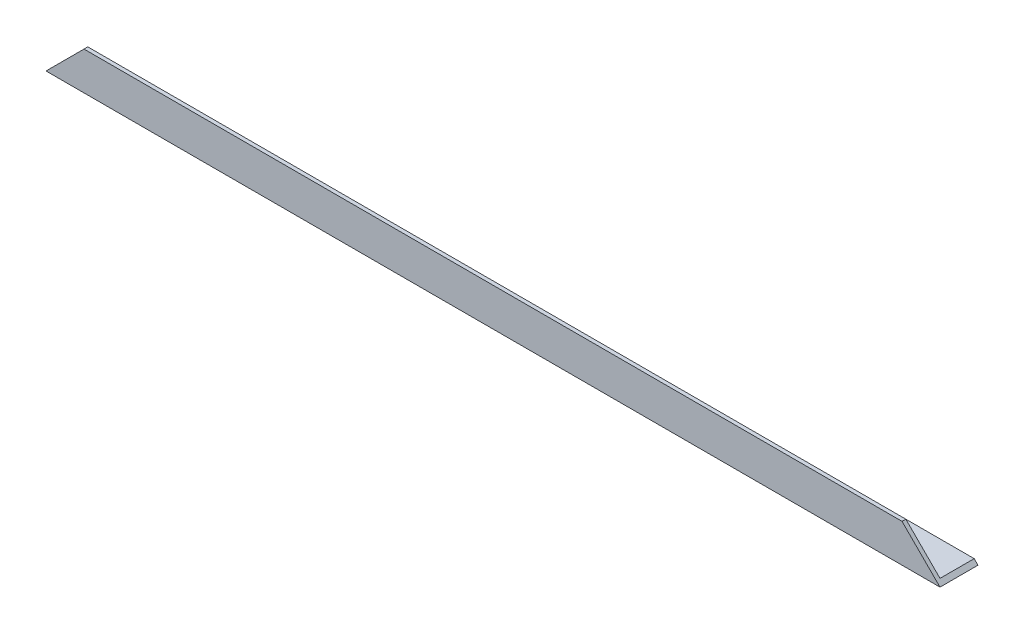
SolidWorks part; units mm, degrees
ref_plane "Спереди" through (0, 0, 0) normal (0, 0, 1) x (1, 0, 0)
ref_plane "Сверху" through (0, 0, 0) normal (0, 1, 0) x (1, 0, 0)
ref_plane "Справа" through (0, 0, 0) normal (1, 0, 0) x (0, 0, -1)
sketch "Эскиз1" plane through (0, 0, 0) normal (1, 0, 0) x (0, 0, -1)
  line L0 (0, 0) -> (0, 15)
  line L1 (0, 15) -> (1.5, 15)
  line L2 (1.5, 15) -> (1.5, 1.5)
  line L3 (1.5, 1.5) -> (15, 1.5)
  line L4 (15, 1.5) -> (15, 0)
  line L5 (15, 0) -> (0, 0)
  dimension "D1" = 15
  dimension "D2" = 15
  dimension "D3" = 1.5
  dimension "D4" = 1.5
extrude "Бобышка-Вытянуть1" add sketch "Эскиз1" along normal blind 353
ref_plane "Плоскость1" through (176.5, 0, 0) normal (-1, 0, 0) x (0, 0, 1)
sketch "Эскиз2" plane through (0, 0, 0) normal (0, 0, 1) x (1, 0, 0)
  line L0 (0, 0) -> (21.7299, 21.7299)
  line L1 (21.7299, 21.7299) -> (0, 21.7299)
  line L2 (0, 21.7299) -> (0, 0)
  dimension "D1" = 45
extrude "Вырез-Вытянуть1" cut sketch "Эскиз2" against normal through all
mirror "Зеркальное отражение1" about plane through (176.5, 0, 0) normal (-1, 0, 0) of "Вырез-Вытянуть1"
